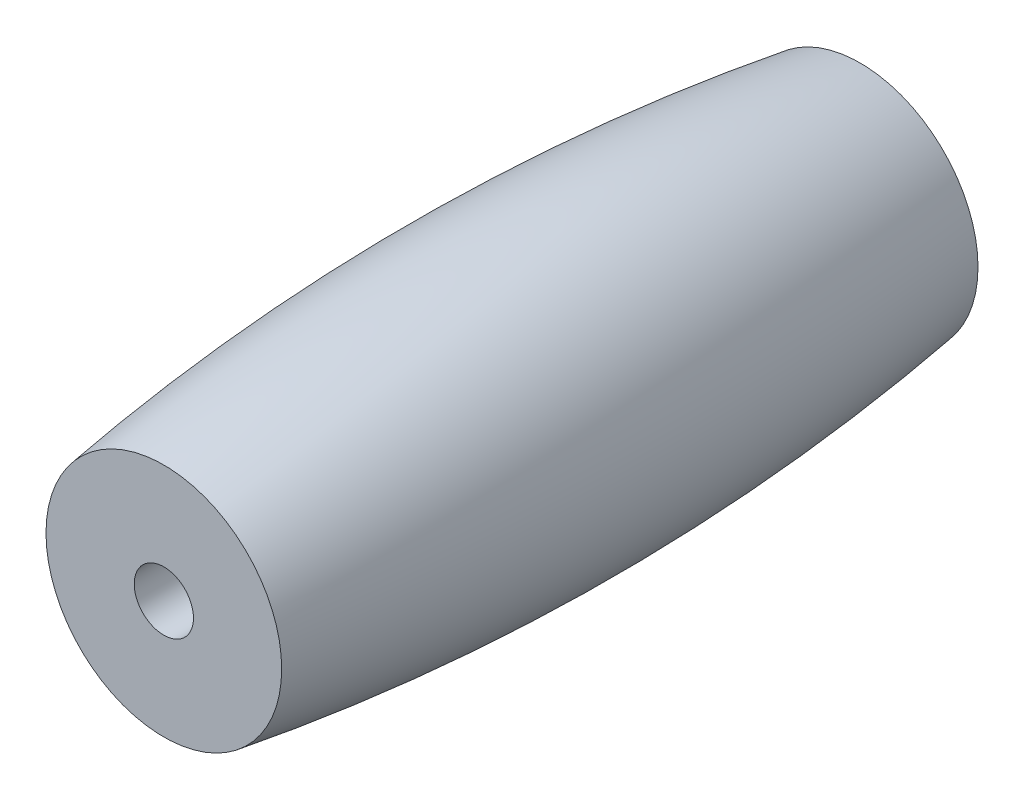
SolidWorks part; units mm, degrees
material "Rubber"
ref_plane "Front Plane" through (0, 0, 0) normal (0, 0, 1) x (1, 0, 0)
ref_plane "Top Plane" through (0, 0, 0) normal (0, 1, 0) x (1, 0, 0)
ref_plane "Right Plane" through (0, 0, 0) normal (1, 0, 0) x (0, 0, -1)
sketch "Sketch2" plane through (0, 0, 0) normal (1, 0, 0) x (0, 0, -1)
  line L0 (0, 0) -> (0, 9.725) construction
  line L1 (-23.5, 0) -> (23.5, 0)
  line L2 (23.5, 0) -> (23.5, 7.954)
  line L3 (0, 9.725) -> (18.9867, 9.725) construction
  line L4 (-23.5, 0) -> (-23.5, 7.954)
  arc A0 (-23.5, 7.954) -> (23.5, 7.954) centre (0, -147.0709) cw
  dimension "D1" = 23.5
ref_axis "Axis1" through (0, 0, -25.85) along (0, 0, 1)
revolve "Revolve1" add sketch "Sketch2" angle 360 about axis through (0, 0, -25.85) along (0, 0, 1)
sketch "Sketch3" plane through (0, 0, 23.5) normal (0, 0, 1) x (1, 0, 0)
  circle A0 centre (0, 0) radius 2
  dimension "D1" = 4
extrude "Cut-Extrude1" cut sketch "Sketch3" against normal through all
